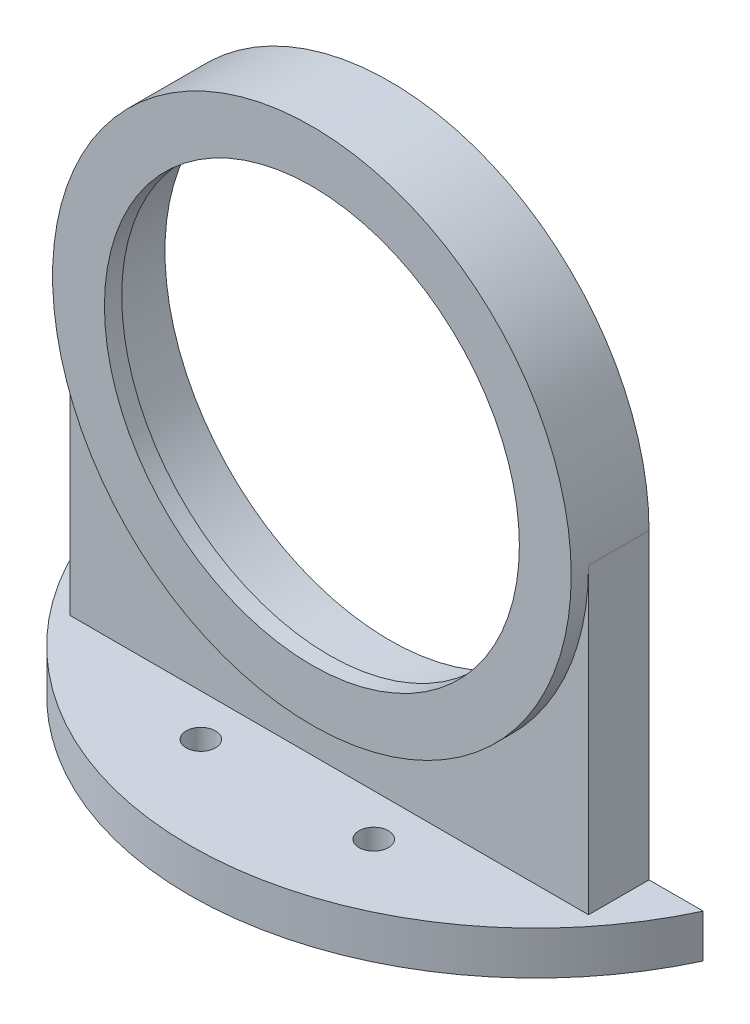
SolidWorks part; units mm, degrees
ref_plane "前视基准面" through (0, 0, 0) normal (0, 0, 1) x (1, 0, 0)
ref_plane "上视基准面" through (0, 0, 0) normal (0, 1, 0) x (1, 0, 0)
ref_plane "右视基准面" through (0, 0, 0) normal (1, 0, 0) x (0, 0, -1)
sketch "草图1" plane through (0, 0, 0) normal (0, 0, 1) x (1, 0, 0)
  line L1 (-15.5, -38) -> (15.5, -38)
  line L2 (-15.5, -38) -> (-15.5, -25.6856)
  line L4 (15.5, -38) -> (15.5, -25.6856)
  line L5 (0, -26) -> (0, -38) construction
  line L6 (-15.5, -31.8428) -> (15.5, -31.8428) construction
  circle A0 centre (0, 0) radius 26
  arc A1 (15.5, -25.6856) -> (-15.5, -25.6856) centre (0, 0) ccw
  point P4 (0, -31.8428)
  dimension "D1" = 52
  dimension "D2" = 60
  dimension "D3" = 31
  dimension "D4" = 38
extrude "凸台-拉伸1" add sketch "草图1" along normal blind 7
sketch "草图3" plane through (0, -38, 0) normal (0, -1, 0) x (1, 0, 0)
  line L0 (0, 0) -> (0, 21.5337) construction
  line L1 (-36.2638, 0) -> (36.2638, 0)
  line L2 (-15.5, 0) -> (15.5, 0) construction
  arc A0 (36.2638, 0) -> (-36.2638, 0) centre (0, -16.88) ccw
  dimension "D3" = 80
  dimension "D2" = 16.88
extrude "凸台-拉伸3" add sketch "草图3" against normal blind 5
sketch "草图4" plane through (0, 0, 7) normal (0, 0, 1) x (1, 0, 0)
  circle A0 centre (0, 0) radius 30
  circle A1 centre (0, 0) radius 24
  dimension "D1" = 60
  dimension "D2" = 48
extrude "凸台-拉伸4" add sketch "草图4" along normal blind 2
sketch "草图5" plane through (0, 0, 0) normal (0, 0, -1) x (-1, 0, 0)
  line L1 (-15.5, -33) -> (-36.2638, -33) construction
  line L2 (-30, -33) -> (-15.5, -33)
  line L3 (-15.5, -33) -> (-15.5, -25.6856)
  line L4 (0, 0) -> (0, 11.9603) construction
  line L5 (15.5, -33) -> (15.5, -25.6856)
  line L6 (30, -33) -> (15.5, -33)
  line L12 (-30, -33) -> (-30, 0)
  line L13 (30, -33) -> (30, 0)
  arc A3 (15.5, -25.6856) -> (-15.5, -25.6856) centre (0, 0) ccw construction
  arc A4 (-30, 0) -> (-15.5, -25.6856) centre (0, 0) ccw
  arc A5 (30, 0) -> (15.5, -25.6856) centre (0, 0) cw
  dimension "D1" = 33
extrude "凸台-拉伸5" add sketch "草图5" against normal up to surface (7 mm away) up to face at (0, -30.4214, 7)
sketch "草图8" plane through (0, -38, 0) normal (0, -1, 0) x (1, 0, 0)
  line L1 (-36.2638, 0) -> (36.2638, 0)
  line L2 (-36.2638, 0) -> (36.2638, 0)
  arc A1 (36.2638, 0) -> (-36.2638, 0) centre (0, -16.88) ccw
  arc A2 (36.2638, 0) -> (-36.2638, 0) centre (0, -16.88) ccw
  dimension "D1" = 0
extrude "凸台-拉伸6" add sketch "草图8" along normal blind 2
sketch "草图9" plane through (0, -33, 0) normal (0, 1, 0) x (1, 0, 0)
  line L5 (30, -7) -> (-30, -7)
  line L6 (-30, -7) -> (-30, 0)
  line L7 (-30, 0) -> (-36.2638, 0)
  line L8 (36.2638, 0) -> (30, 0)
  line L9 (30, 0) -> (30, -7)
  line L10 (30, -7) -> (-30, -7)
  line L11 (-30, -7) -> (-30, 0)
  line L12 (-30, 0) -> (-36.2638, 0)
  line L13 (36.2638, 0) -> (30, 0)
  line L14 (30, 0) -> (30, -7)
  arc A1 (-36.2638, 0) -> (36.2638, 0) centre (0, 16.88) ccw
  arc A2 (-36.2638, 0) -> (36.2638, 0) centre (0, 16.88) ccw
  dimension "D1" = 0
extrude "切除-拉伸2" cut sketch "草图9" against normal blind 2
sketch "草图11" plane through (0, -35, 0) normal (0, 1, 0) x (1, 0, 0)
  line L0 (30, 0) -> (-30, 0) construction
  line L1 (0, 7.8922) -> (0, -32.6645) construction
  circle A0 centre (-10, -11.85) radius 1.7
  circle A1 centre (10, -11.85) radius 1.7
  dimension "D2" = 3.4
  dimension "D3" = 20
  dimension "D1" = 11.85
extrude "切除-拉伸3" cut sketch "草图11" against normal blind 10
